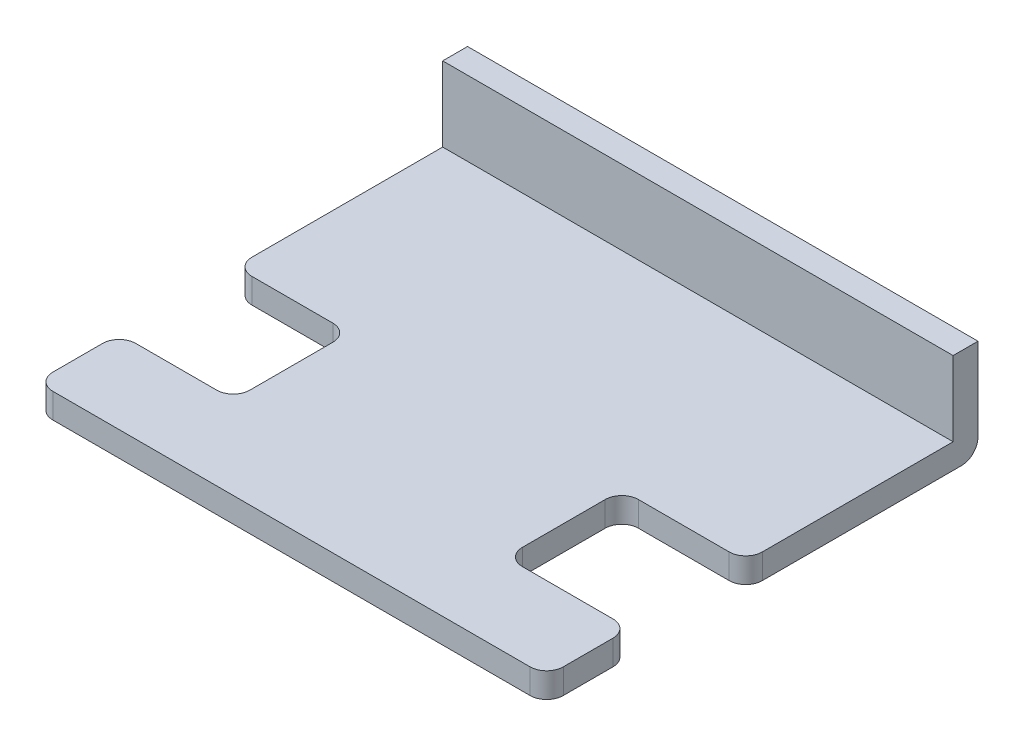
SolidWorks part; units mm, degrees
ref_plane "Front Plane" through (0, 0, 0) normal (0, 0, 1) x (1, 0, 0)
ref_plane "Top Plane" through (0, 0, 0) normal (0, 1, 0) x (1, 0, 0)
ref_plane "Right Plane" through (0, 0, 0) normal (1, 0, 0) x (0, 0, -1)
sketch "Sketch1" plane through (0, 0, 0) normal (0, 1, 0) x (1, 0, 0)
  line L0 (18.1243, -19.787) -> (29.0651, -19.787)
  line L1 (-30.4734, 5.213) -> (31.0651, 5.213)
  line L2 (-30.4734, 5.213) -> (-30.4734, -17.787)
  line L3 (-28.4734, -19.787) -> (-18.716, -19.787)
  line L4 (31.0651, 5.213) -> (31.0651, -17.787)
  line L6 (-16.716, -21.787) -> (-16.716, -31.787)
  line L8 (16.1243, -21.787) -> (16.1243, -31.787)
  line L9 (-28.4734, -33.787) -> (-18.716, -33.787)
  line L10 (-30.4734, -35.787) -> (-30.4734, -41.787)
  line L11 (-28.4734, -43.787) -> (29.0651, -43.787)
  line L12 (31.0651, -35.787) -> (31.0651, -41.787)
  line L13 (18.1243, -33.787) -> (29.0651, -33.787)
  arc A0 (29.0651, -19.787) -> (31.0651, -17.787) centre (29.0651, -17.787) ccw
  arc A1 (-30.4734, -17.787) -> (-28.4734, -19.787) centre (-28.4734, -17.787) ccw
  arc A2 (-28.4734, -33.787) -> (-30.4734, -35.787) centre (-28.4734, -35.787) ccw
  arc A3 (-30.4734, -41.787) -> (-28.4734, -43.787) centre (-28.4734, -41.787) ccw
  arc A4 (29.0651, -43.787) -> (31.0651, -41.787) centre (29.0651, -41.787) ccw
  arc A5 (29.0651, -33.787) -> (31.0651, -35.787) centre (29.0651, -35.787) cw
  arc A6 (18.1243, -33.787) -> (16.1243, -31.787) centre (18.1243, -31.787) cw
  arc A7 (-18.716, -33.787) -> (-16.716, -31.787) centre (-18.716, -31.787) ccw
  arc A8 (16.1243, -21.787) -> (18.1243, -19.787) centre (18.1243, -21.787) cw
  arc A9 (-16.716, -21.787) -> (-18.716, -19.787) centre (-18.716, -21.787) ccw
  point P16 (-30.4734, -19.787)
  point P23 (31.0651, -43.787)
  point P26 (31.0651, -33.787)
  point P31 (-16.716, -33.787)
  point P36 (-16.716, -19.787)
  dimension "D4" = 2
  dimension "D1" = 25
  dimension "D2" = 14
  dimension "D3" = 10
  dimension "D5" = 32.8402
extrude "Boss-Extrude1" add sketch "Sketch1" along normal blind 3
sketch "Sketch2" plane through (0, 0, -5.213) normal (0, 0, -1) x (-1, 0, 0)
  line L1 (-31.0651, 0) -> (30.4734, 0)
  line L2 (-31.0651, 0) -> (-31.0651, 12)
  line L3 (-31.0651, 12) -> (30.4734, 12)
  line L4 (30.4734, 0) -> (30.4734, 12)
  dimension "D1" = 12
extrude "Boss-Extrude2" add sketch "Sketch2" along normal blind 3
fillet "Fillet1" radius 2 1 edges at (0.2959, 0, -8.213)
